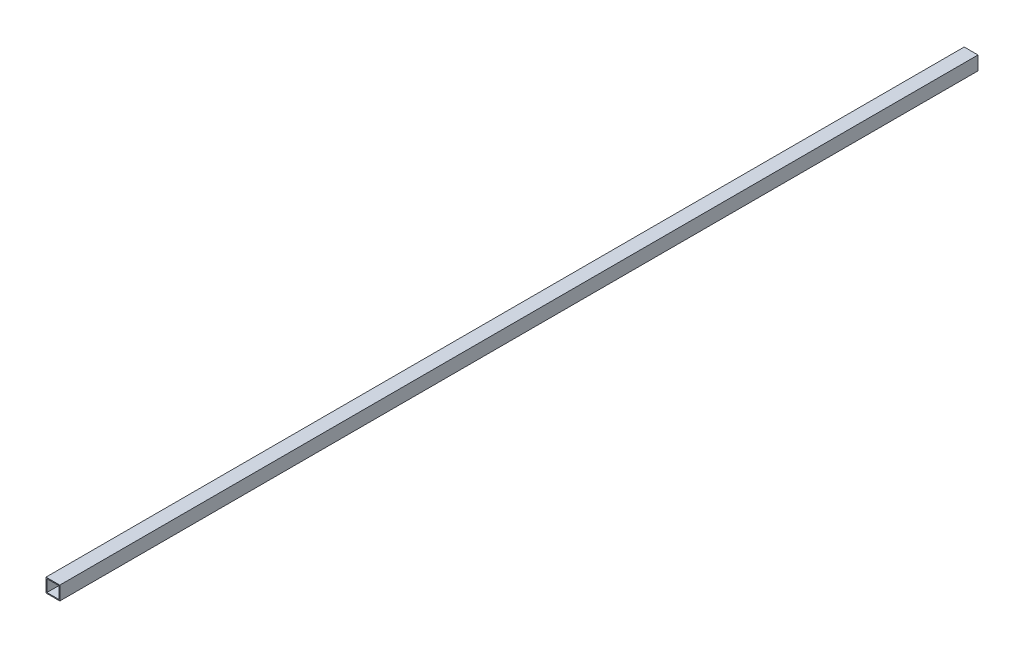
SolidWorks part; units mm, degrees
ref_plane "Front Plane" through (0, 0, 0) normal (0, 0, 1) x (1, 0, 0)
ref_plane "Top Plane" through (0, 0, 0) normal (0, 1, 0) x (1, 0, 0)
ref_plane "Right Plane" through (0, 0, 0) normal (1, 0, 0) x (0, 0, -1)
sketch "Sketch1" plane through (0, 0, 0) normal (0, 0, 1) x (1, 0, 0)
  line L0 (13, 13) -> (-13, 13)
  line L1 (15, 15) -> (-15, 15)
  line L2 (15, 15) -> (15, -15)
  line L3 (15, -15) -> (-15, -15)
  line L4 (-15, 15) -> (-15, -15)
  line L5 (15, 15) -> (-15, -15) construction
  line L6 (15, -15) -> (-15, 15) construction
  line L7 (-13, 13) -> (-13, -13)
  line L8 (13, -13) -> (-13, -13)
  line L9 (13, 13) -> (13, -13)
  point P0 (0, 0)
  dimension "D1" = 30
  dimension "D2" = 30
  dimension "D3" = 2
extrude "Boss-Extrude1" add sketch "Sketch1" along normal blind 1995.5
